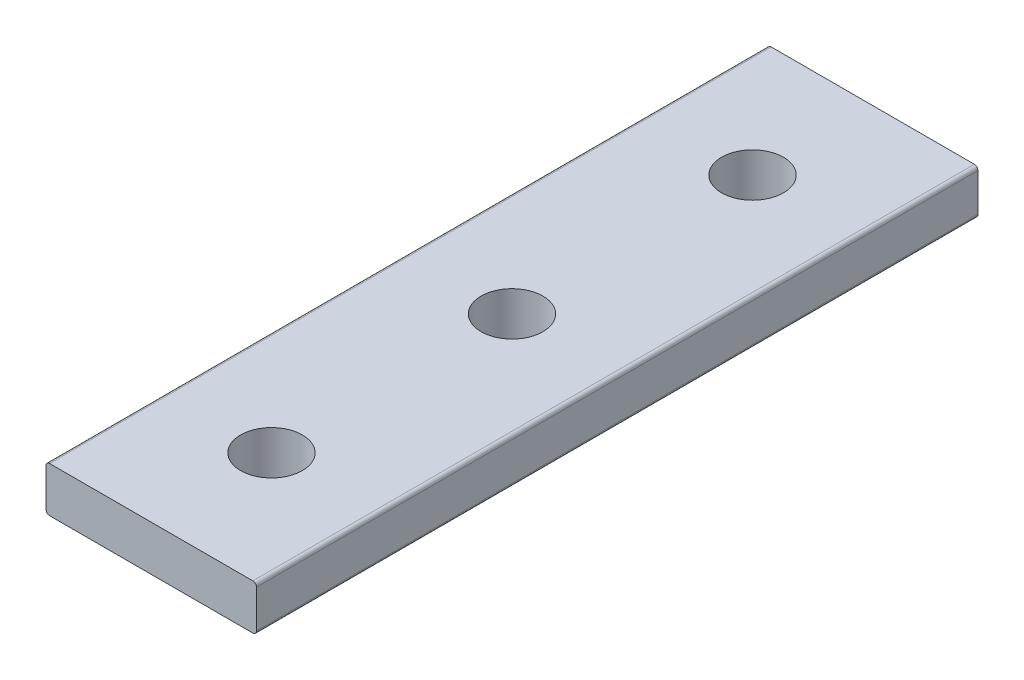
SolidWorks part; units mm, degrees
material "6105-T5 Aluminum"
ref_plane "Front Plane" through (0, 0, 0) normal (0, 0, 1) x (1, 0, 0)
ref_plane "Top Plane" through (0, 0, 0) normal (0, 1, 0) x (1, 0, 0)
ref_plane "Right Plane" through (0, 0, 0) normal (1, 0, 0) x (0, 0, -1)
ref_plane "Plane1" through (0, 4.7752, 0) normal (0, 1, 0) x (1, 0, 0)
sketch "Sketch1" plane through (0, 4.7752, 0) normal (0, 1, 0) x (1, 0, 0)
  line L0 (22.225, 0) -> (0, 0)
  line L1 (0, 0) -> (0, -76.2)
  line L2 (0, -76.2) -> (22.225, -76.2)
  line L3 (22.225, -76.2) -> (22.225, 0)
extrude "Boss-Extrude1" add sketch "Sketch1" against normal blind 4.7752
hole_wizard "F (0.257) Diameter Hole1" positions "Sketch3" profile "Sketch2" hole size "F" standard "ANSI Inch" end condition through all
sketch "Sketch3" plane through (0, 0, 0) normal (0, -1, 0) x (-1, 0, 0)
  line L0 (0, 0) -> (0, -76.2) construction
  point P0 (-11.1125, -12.7)
  point P1 (-11.1125, -38.1)
  point P2 (-11.1125, -63.5)
  dimension "D1" = 25.4
  dimension "D2" = 25.4
  dimension "D3" = 11.1125
sketch "Sketch2" plane through (11.1125, 0, 12.7) normal (1, 0, 0) x (0, 0, -1)
  line L0 (0, 0) -> (0, 4.7752)
  line L1 (0, 4.7752) -> (3.2639, 4.7752)
  line L2 (3.2639, 4.7752) -> (3.2639, 0)
  line L5 (3.2639, 0) -> (0, 0)
  line L11 (0, -6.35) -> (0, 107.95) construction
  dimension "Thru Hole Dia." = 6.5278
  dimension "Thru Hole Depth" = 4.7752
fillet "Fillet1" radius 0.381 4 edges at (22.225, 0, 38.1) (0, 0, 38.1) (22.225, 4.7752, 38.1) (0, 4.7752, 38.1)
ref_plane "Plane2" through (11.1125, 0, 0) normal (1, 0, 0) x (0, 0, -1)
